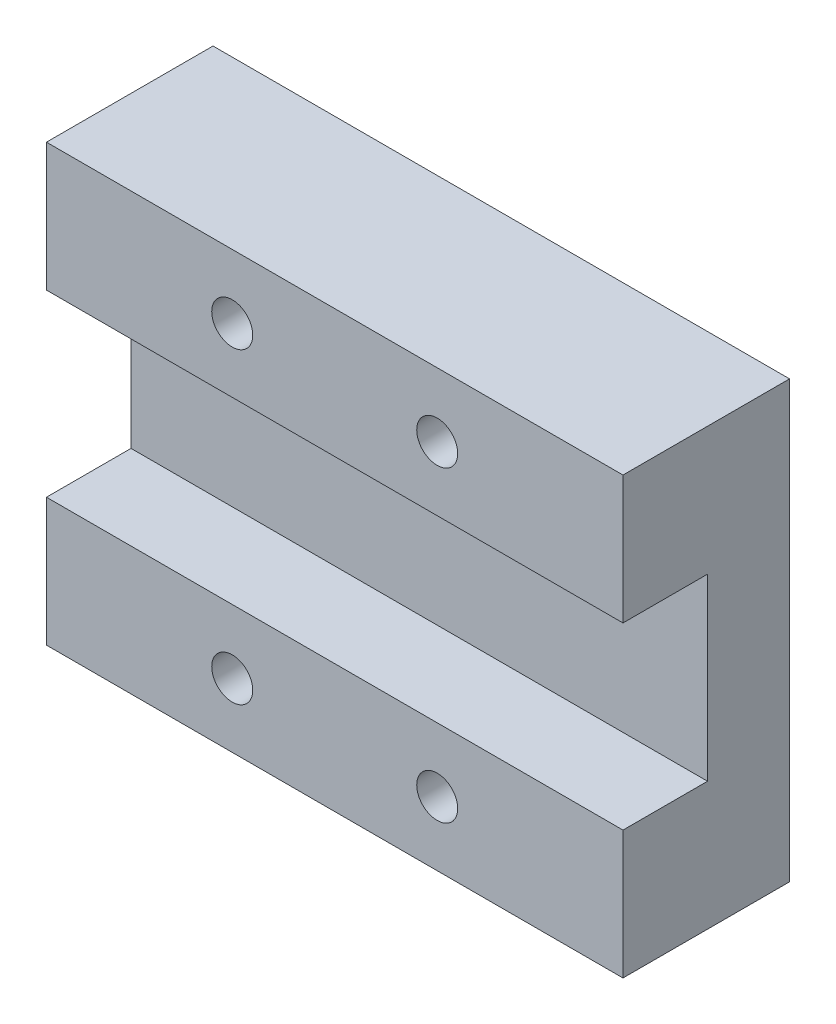
SolidWorks part; units mm, degrees
ref_plane "前视基准面" through (0, 0, 0) normal (0, 0, 1) x (1, 0, 0)
ref_plane "上视基准面" through (0, 0, 0) normal (0, 1, 0) x (1, 0, 0)
ref_plane "右视基准面" through (0, 0, 0) normal (1, 0, 0) x (0, 0, -1)
sketch "草图1" plane through (0, 0, 0) normal (0, 0, 1) x (1, 0, 0)
  line L1 (0, 0) -> (22.5, 0)
  line L2 (0, 0) -> (0, 17)
  line L3 (0, 17) -> (22.5, 17)
  line L4 (22.5, 0) -> (22.5, 17)
  dimension "D1" = 22.5
  dimension "D2" = 17
extrude "凸台-拉伸1" add sketch "草图1" along normal blind 6.5
sketch "草图2" plane through (0, 0, 0) normal (-1, 0, 0) x (0, 0, 1)
  line L0 (0, 8.5) -> (6.5, 8.5) construction
  line L1 (0, 17) -> (0, 0) construction
  line L2 (6.5, 17) -> (6.5, 0) construction
  line L4 (6.5, 5) -> (3.2, 5)
  line L5 (6.5, 5) -> (6.5, 12)
  line L6 (6.5, 12) -> (3.2, 12)
  line L7 (3.2, 5) -> (3.2, 12)
  dimension "D1" = 3.2
  dimension "D2" = 7
extrude "切除-拉伸1" cut sketch "草图2" against normal through all
hole_wizard "M2 螺纹孔1" positions "草图3" profile "草图4" tap size "M2" standard "ISO"
sketch "草图3" plane through (0, 0, 0) normal (0, 0, -1) x (-1, 0, 0)
  line L0 (-22.5, 8.5) -> (0, 8.5) construction
  line L1 (-22.5, 0) -> (-22.5, 17) construction
  line L2 (0, 17) -> (0, 0) construction
  line L3 (0, 8.5) -> (-11.25, 8.5) construction
  line L4 (-11.25, 8.5) -> (-11.25, 17) construction
  line L5 (-22.5, 17) -> (0, 17) construction
  point P0 (-15.25, 2.5)
  point P2 (-7.25, 2.5)
  point P4 (-15.25, 14.5)
  point P6 (-7.25, 14.5)
  point P20 (0, 0)
  point P21 (0, 0)
  dimension "D1" = 12
  dimension "D2" = 8
sketch "草图4" plane through (15.25, 2.5, 0) normal (1, 0, 0) x (0, 1, 0)
  line L0 (0, 0) -> (0, 10.5807)
  line L1 (0, 10.5807) -> (0.8, 10.1)
  line L2 (0.8, 10.1) -> (0.8, 0)
  line L5 (0.8, 0) -> (0, 0)
  line L10 (0, 10.5807) -> (-0.8, 10.1) construction
  line L11 (0, -6.35) -> (0, 107.95) construction
  dimension "螺纹孔钻头直径" = 1.6
  dimension "螺纹孔钻头深度" = 10.1
  dimension "导头角度" = 118
cosmetic thread "孔螺蚊线1" parameters "D1"=4, "D2"=2
cosmetic thread "孔螺蚊线2" parameters "D1"=4, "D2"=2
cosmetic thread "孔螺蚊线3" parameters "D1"=4, "D2"=2
cosmetic thread "孔螺蚊线4" parameters "D1"=4, "D2"=2
